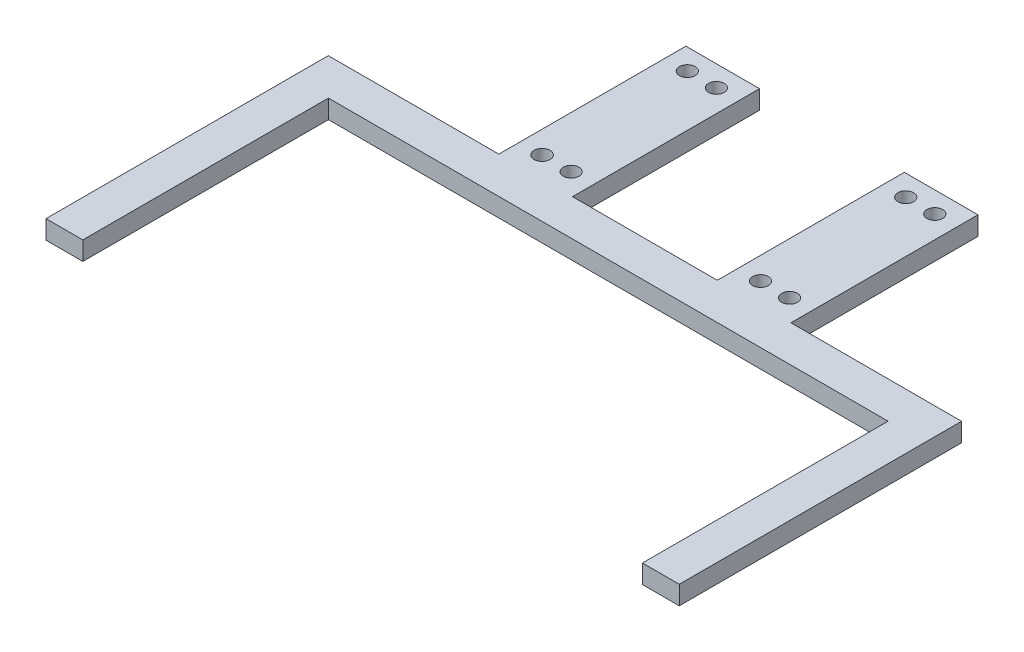
SolidWorks part; units mm, degrees
ref_plane "Front Plane" through (0, 0, 0) normal (0, 0, 1) x (1, 0, 0)
ref_plane "Top Plane" through (0, 0, 0) normal (0, 1, 0) x (1, 0, 0)
ref_plane "Right Plane" through (0, 0, 0) normal (1, 0, 0) x (0, 0, -1)
sketch "Sketch1" plane through (0, 0, 0) normal (0, 1, 0) x (1, 0, 0)
  line L0 (19.2949, -16.615) -> (19.2949, 79.2236)
  line L1 (19.2949, 79.2236) -> (77.2109, 79.2236)
  line L2 (77.2109, 79.2236) -> (77.2109, 142.7236)
  line L3 (77.2109, 142.7236) -> (102.2109, 142.7236)
  line L4 (102.2109, 142.7236) -> (102.2109, 79.2236)
  line L5 (102.2109, 79.2236) -> (151.3789, 79.2236)
  line L6 (151.3789, 79.2236) -> (151.3789, 142.7236)
  line L7 (151.3789, 142.7236) -> (176.3789, 142.7236)
  line L8 (176.3789, 142.7236) -> (176.3789, 79.2236)
  line L9 (176.3789, 79.2236) -> (234.2949, 79.2236)
  line L10 (234.2949, 79.2236) -> (234.2949, -16.615)
  line L11 (234.2949, -16.615) -> (221.7949, -16.615)
  line L12 (221.7949, -16.615) -> (221.7949, 66.7776)
  line L13 (221.7949, 66.7776) -> (31.7949, 66.7776)
  line L14 (31.7949, 66.7776) -> (31.7949, -16.615)
  line L15 (31.7949, -16.615) -> (19.2949, -16.615)
  line L16 (89.7109, 142.7236) -> (89.7109, 66.7776) construction
  line L17 (163.8789, 142.7236) -> (163.8789, 66.7776) construction
  line L18 (84.7799, 135.6236) -> (94.6499, 135.6236) construction
  line L19 (158.9399, 135.6236) -> (168.8099, 135.6236) construction
  dimension "D1" = 190
  dimension "D2" = 12.5
  dimension "D3" = 74.168
  dimension "D4" = 25
  dimension "D5" = 12.446
  dimension "D6" = 12.446
  dimension "D7" = 63.5
extrude "Boss-Extrude1" add sketch "Sketch1" along normal blind 6.35
sketch "Sketch3" plane through (0, 0, 0) normal (0, -1, 0) x (1, 0, 0)
  circle A0 centre (84.7799, -86.3236) radius 2.713
  circle A1 centre (94.6499, -86.3236) radius 2.663
  circle A2 centre (84.7799, -135.6236) radius 2.663
  circle A3 centre (94.6499, -135.6236) radius 2.663
  circle A4 centre (158.9399, -86.3236) radius 2.663
  circle A5 centre (168.8099, -86.3236) radius 2.663
  circle A6 centre (158.9399, -135.6236) radius 2.663
  circle A7 centre (168.8099, -135.6236) radius 2.663
  dimension "D1" = 5.426
  dimension "D2" = 5.326
  dimension "D3" = 5.326
  dimension "D4" = 5.326
  dimension "D5" = 5.326
  dimension "D6" = 5.326
  dimension "D7" = 5.326
  dimension "D8" = 5.326
extrude "Cut-Extrude1" cut sketch "Sketch3" against normal up to surface (6.35 mm away) up to face at (126.7949, 6.35, -69.5832)
